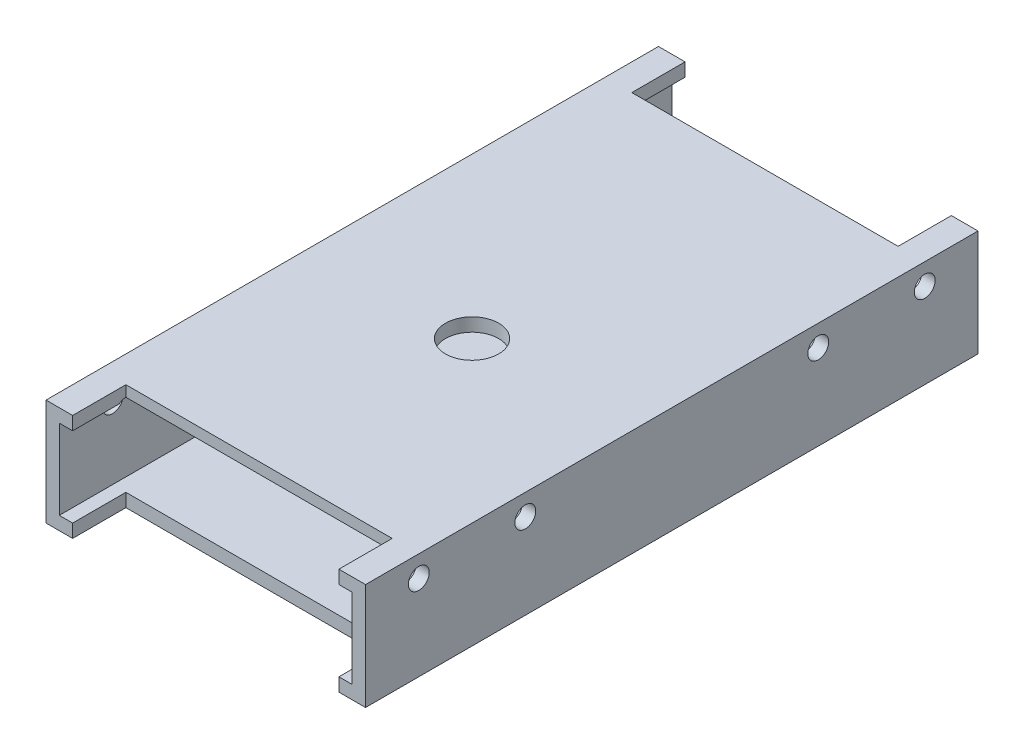
SolidWorks part; units mm, degrees
ref_plane "Front" through (0, 0, 0) normal (0, 0, 1) x (1, 0, 0)
ref_plane "Top" through (0, 0, 0) normal (0, 1, 0) x (1, 0, 0)
ref_plane "Right" through (0, 0, 0) normal (1, 0, 0) x (0, 0, -1)
sketch "Sketch1" plane through (0, 0, 0) normal (0, 0, 1) x (1, 0, 0)
  line L1 (-38.1, -12.7) -> (38.1, -12.7)
  line L2 (-38.1, -12.7) -> (-38.1, 12.7)
  line L3 (-38.1, 12.7) -> (38.1, 12.7)
  line L4 (38.1, -12.7) -> (38.1, 12.7)
  line L5 (-38.1, -12.7) -> (38.1, 12.7) construction
  line L6 (-38.1, 12.7) -> (38.1, -12.7) construction
  point P0 (0, 0)
  dimension "D1" = 25.4
  dimension "D2" = 76.2
extrude "Extrude-Thin1" add sketch "Sketch1" along normal mid plane 146.05 thin thin type one direction reverse wall 3.175
sketch "Sketch2" plane through (0, -12.7, 0) normal (0, -1, 0) x (1, 0, 0)
  line L0 (31.75, -73.025) -> (31.75, -60.325)
  line L1 (-38.1, -73.025) -> (38.1, -73.025) construction
  line L2 (31.75, -60.325) -> (-31.75, -60.325)
  line L3 (-31.75, -60.325) -> (-31.75, -73.025)
  line L4 (-38.1, 0) -> (38.1, 0) construction
  line L5 (-38.1, 73.025) -> (-38.1, -73.025) construction
  line L6 (38.1, 73.025) -> (38.1, -73.025) construction
  line L7 (0, -60.325) -> (0, -73.025) construction
  line L8 (-31.75, 60.325) -> (-31.75, 73.025)
  line L9 (31.75, 73.025) -> (31.75, 60.325)
  line L10 (31.75, 60.325) -> (-31.75, 60.325)
  line M5 (-38.1, -73.025) -> (38.1, -73.025)
  line M7 (38.1, 73.025) -> (-38.1, 73.025)
  dimension "D1" = 6.35
  dimension "D3" = 12.7
extrude "Cut-Extrude1" cut sketch "Sketch2" against normal through all contours L2 L3 L0 M5 | L10 L9 L8 M7
sketch "Sketch3" plane through (38.1, 0, 0) normal (1, 0, 0) x (0, 0, -1)
  line L0 (73.025, 7.62) -> (-73.025, 7.62) construction
  line L1 (-73.025, 12.7) -> (73.025, 12.7) construction
  line L4 (73.025, -12.7) -> (73.025, 12.7) construction
  line L5 (-73.025, 12.7) -> (73.025, 12.7) construction
  line L6 (-73.025, -12.7) -> (-73.025, 12.7) construction
  line L7 (0, -12.7) -> (0, 12.7) construction
  line L8 (-73.025, -12.7) -> (73.025, -12.7) construction
  circle A0 centre (60.325, 7.62) radius 2.4892
  circle A3 centre (34.925, 7.62) radius 2.4892
  circle A4 centre (-34.925, 7.62) radius 2.4892
  circle A5 centre (-60.325, 7.62) radius 2.4892
  point P14 (60.325, 10.1092)
  dimension "D1" = 25.4
  dimension "D3" = 4.9784
  dimension "D2" = 12.7
  dimension "D4" = 5.08
extrude "Cut-Extrude2" cut sketch "Sketch3" against normal through all and the other way through all
sketch "Sketch4" plane through (0, -12.7, 0) normal (0, -1, 0) x (1, 0, 0)
  line L0 (0, 9.525) -> (0, -73.025) construction
  line L1 (-31.75, -73.025) -> (31.75, -73.025) construction
  circle A0 centre (0, 9.525) radius 6.35
  dimension "D1" = 63.5
  dimension "D2" = 12.7
extrude "Cut-Extrude3" cut sketch "Sketch4" against normal through all
